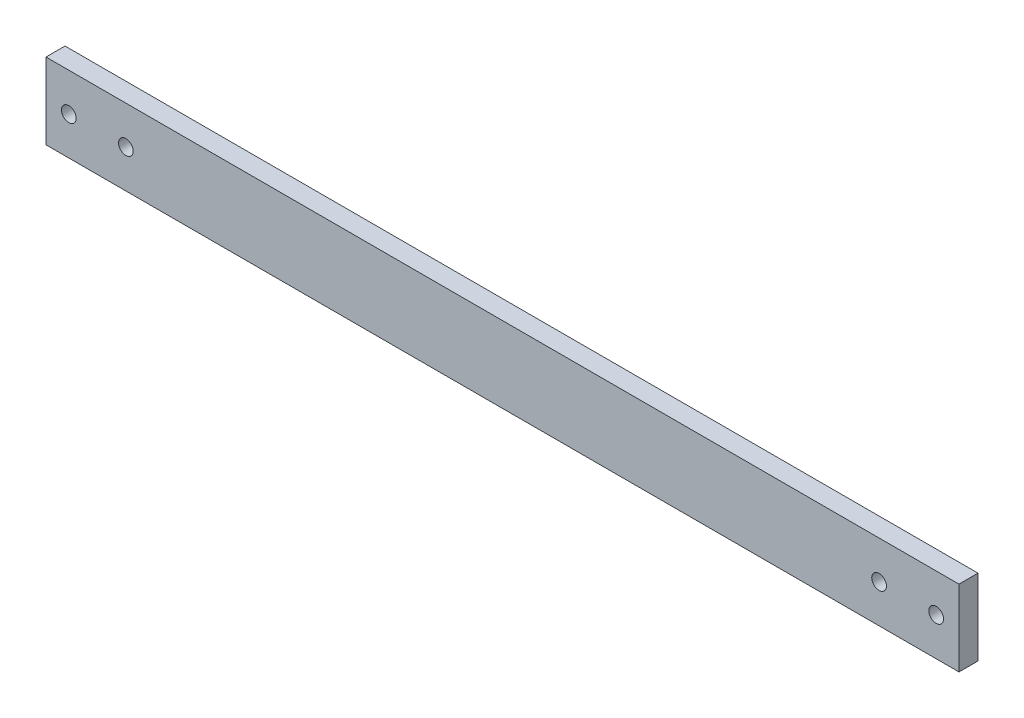
SolidWorks part; units mm, degrees
material "1060 Alloy"
ref_plane "Front" through (0, 0, 0) normal (0, 0, 1) x (1, 0, 0)
ref_plane "Top" through (0, 0, 0) normal (0, 1, 0) x (1, 0, 0)
ref_plane "Right" through (0, 0, 0) normal (1, 0, 0) x (0, 0, -1)
sketch "Sketch1" plane through (0, 0, 0) normal (0, 0, 1) x (1, 0, 0)
  line L1 (0, 12.7) -> (304.8, 12.7)
  line L2 (0, 12.7) -> (0, -12.7)
  line L3 (0, -12.7) -> (304.8, -12.7)
  line L4 (304.8, 12.7) -> (304.8, -12.7)
  point P4 (0, 0)
  dimension "D1" = 25.4
  dimension "D2" = 304.8
extrude "Boss-Extrude1" add sketch "Sketch1" along normal mid plane 6.35
sketch "Sketch2" plane through (0, 0, 3.175) normal (0, 0, 1) x (1, 0, 0)
  line L0 (0, 12.7) -> (0, -12.7) construction
  line L1 (304.8, -12.7) -> (304.8, 12.7) construction
  point P0 (7.62, 0)
  point P3 (26.67, 0)
  point P4 (297.18, 0)
  point P5 (278.13, 0)
  dimension "D1" = 7.62
  dimension "D2" = 19.05
  dimension "D3" = 7.62
  dimension "D4" = 19.05
hole_wizard "#10 (0.1935) Diameter Hole1" positions "Sketch5" profile "Sketch4" hole size "#10" standard "ANSI Inch"
sketch "Sketch5" plane through (0, 0, 3.175) normal (0, 0, 1) x (1, 0, 0)
  point P0 (7.62, 0)
  point P3 (26.67, 0)
  point P7 (278.13, 0)
  point P10 (297.18, 0)
sketch "Sketch4" plane through (7.62, 0, 3.175) normal (1, 0, 0) x (0, -1, 0)
  line L0 (0, 0) -> (0, 13.4146)
  line L1 (0, 13.4146) -> (2.4574, 11.938)
  line L2 (2.4574, 11.938) -> (2.4574, 0)
  line L5 (2.4574, 0) -> (0, 0)
  line L10 (0, 13.4146) -> (-2.4574, 11.938) construction
  line L11 (0, -6.35) -> (0, 107.95) construction
  dimension "Hole Dia." = 4.9149
  dimension "Hole Depth" = 11.938
  dimension "Drill Angle" = 118
